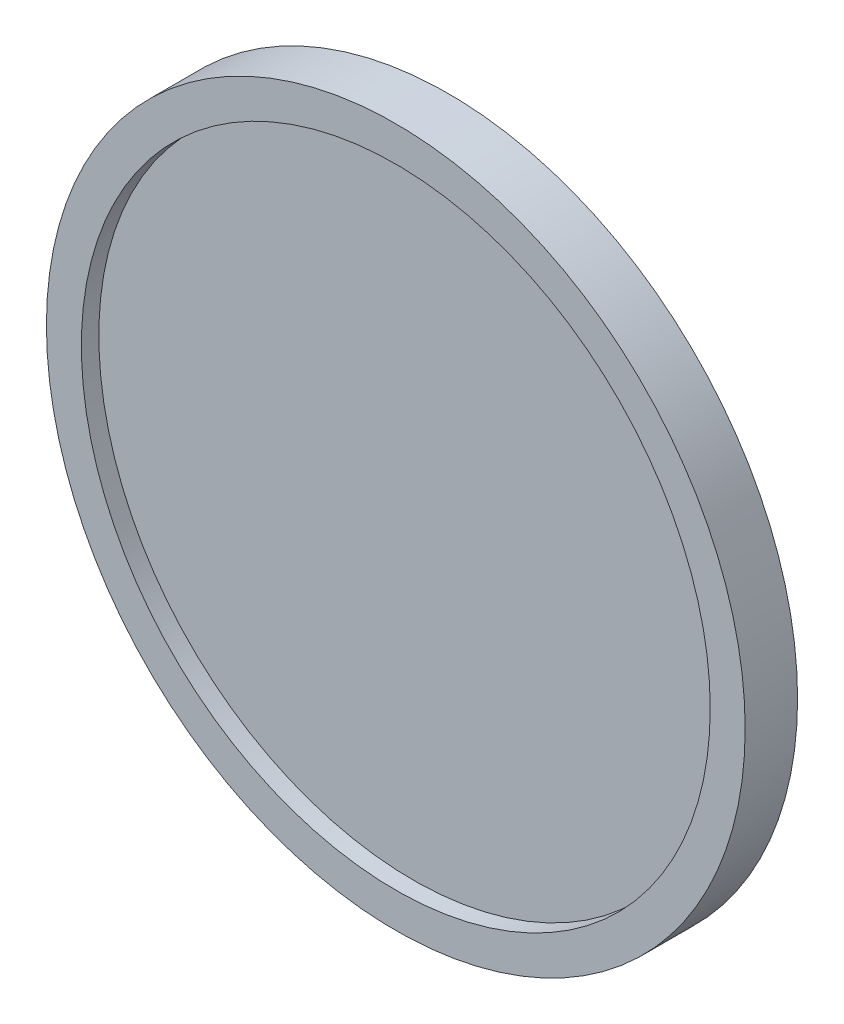
SolidWorks part; units mm, degrees
ref_plane "前视基准面" through (0, 0, 0) normal (0, 0, 1) x (1, 0, 0)
ref_plane "上视基准面" through (0, 0, 0) normal (0, 1, 0) x (1, 0, 0)
ref_plane "右视基准面" through (0, 0, 0) normal (1, 0, 0) x (0, 0, -1)
sketch "草图1" plane through (0, 0, 0) normal (0, 0, 1) x (1, 0, 0)
  circle A0 centre (0, 0) radius 20
extrude "凸台-拉伸1" add sketch "草图1" along normal blind 2
sketch "草图2" plane through (0, 0, 2) normal (0, 0, 1) x (1, 0, 0)
  circle A0 centre (0, 0) radius 20
  circle A1 centre (0, 0) radius 18
extrude "凸台-拉伸2" add sketch "草图2" along normal blind 1
